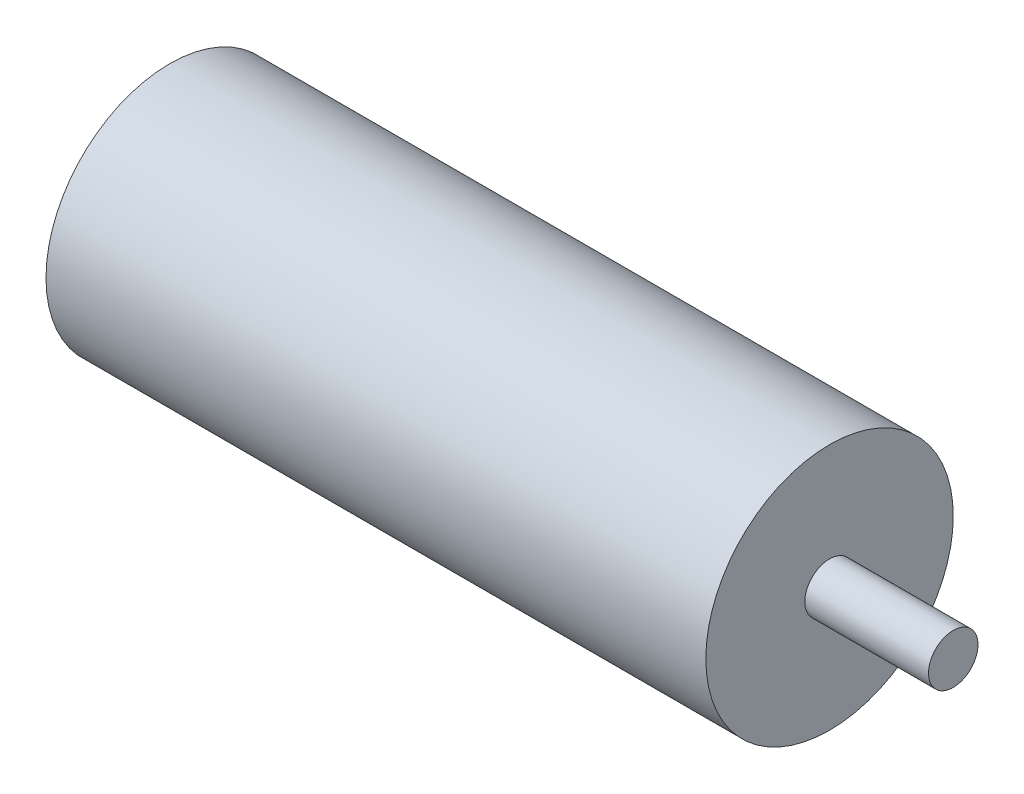
SolidWorks part; units mm, degrees
ref_plane "Front Plane" through (0, 0, 0) normal (0, 0, 1) x (1, 0, 0)
ref_plane "Top Plane" through (0, 0, 0) normal (0, 1, 0) x (1, 0, 0)
ref_plane "Right Plane" through (0, 0, 0) normal (1, 0, 0) x (0, 0, -1)
sketch "Sketch1" plane through (0, 0, 0) normal (1, 0, 0) x (0, 0, -1)
  circle A0 centre (-35.8177, 20.0994) radius 7.5
  dimension "D1" = 15
extrude "Boss-Extrude1" add sketch "Sketch1" along normal blind 45
sketch "Sketch2" plane through (45, 0, 0) normal (1, 0, 0) x (0, 0, -1)
  circle A0 centre (-35.8177, 20.0994) radius 1.5
extrude "Boss-Extrude2" add sketch "Sketch2" along normal blind 15
sketch "Sketch3" plane through (60, 0, 0) normal (1, 0, 0) x (0, 0, -1)
  circle A0 centre (-35.7612, 20.1498) radius 3.3895
extrude "Cut-Extrude1" cut sketch "Sketch3" against normal blind 7.5
sketch "Sketch4" plane through (0, 0, 0) normal (-1, 0, 0) x (0, 0, 1)
  circle A0 centre (34.8497, 19.4638) radius 13.0892
extrude "Cut-Extrude2" cut sketch "Sketch4" against normal blind 5
